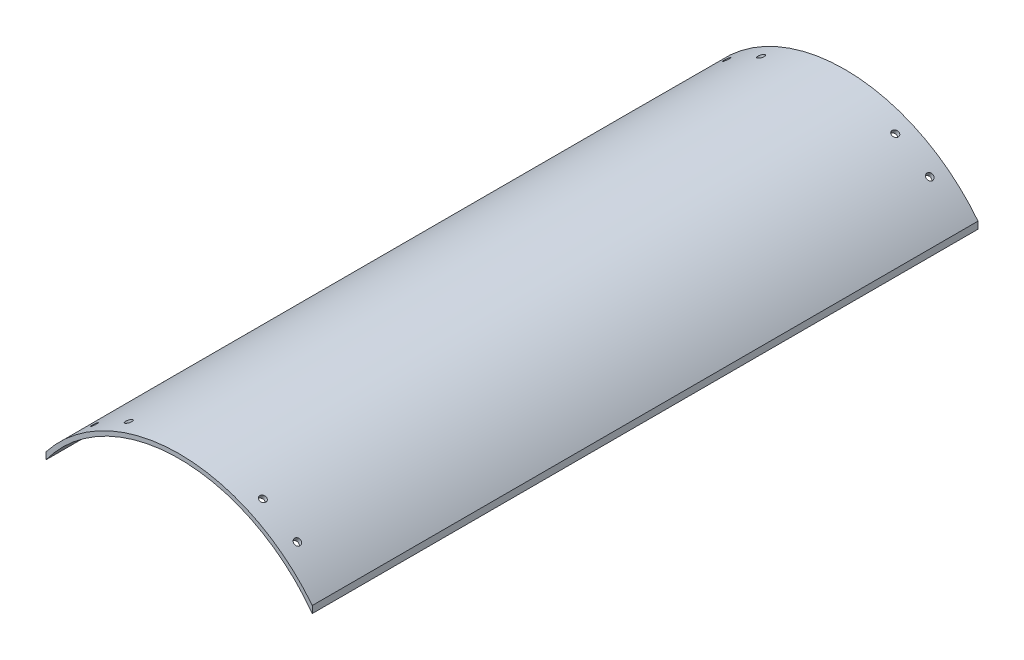
SolidWorks part; units mm, degrees
ref_plane "Front Plane" through (0, 0, 0) normal (0, 0, 1) x (1, 0, 0)
ref_plane "Top Plane" through (0, 0, 0) normal (0, 1, 0) x (1, 0, 0)
ref_plane "Right Plane" through (0, 0, 0) normal (1, 0, 0) x (0, 0, -1)
sketch "Sketch1" plane through (0, 0, 0) normal (0, 0, 1) x (1, 0, 0)
  line L0 (-40, 29.2099) -> (40, 29.2099)
  line L1 (-40, 29.2099) -> (-40, 31.3152)
  line L2 (40, 29.2099) -> (40, 31.3152)
  circle A0 centre (0, 0) radius 49.53
  circle A1 centre (0, 0) radius 50.8
  dimension "D1" = 101.6
  dimension "D2" = 1.27
  dimension "D3" = 80
extrude "Boss-Extrude1" add sketch "Sketch1" along normal blind 200 contours L2 A1 L1 A0
ref_plane "Plane2" through (0, 50.8, 0) normal (0, 1, 0) x (1, 0, 0)
ref_plane "Plane3" through (0, 0, 100) normal (0, 0, 1) x (1, 0, 0)
sketch "Sketch5" plane through (-693.2227, -633.3072, 0) normal (-0.7152, 0.6989, 0) x (0.6989, 0.7152, 0)
  line L0 (986.9759, 0) -> (930.3824, 0) construction
  line L3 (986.9759, 0) -> (930.3824, 0)
  line L8 (931.8881, -200) -> (931.8881, 0) construction
  line L9 (931.8881, -200) -> (931.8881, 0)
  circle A0 centre (937.4459, -144.6) radius 1.5
  circle A1 centre (937.4459, -170) radius 1.5
  circle A2 centre (937.4459, -30) radius 1.5
  circle A3 centre (937.4459, -55.4) radius 1.5
  point P4 (937.4222, -170)
  point P5 (940.8131, -170)
  point P12 (937.4459, -170)
  dimension "D1" = 3
  dimension "D2" = 25.4
  dimension "D4" = 30
  dimension "D5" = 25.4
  dimension "D6" = 30
extrude "Cut-Extrude2" cut sketch "Sketch5" against normal blind 9 contours A2 | A3 | A0 | A1 | A3 | A0 | A1
sketch "Sketch6" plane through (24.1451, 41.5821, -52.4) normal (-0.5021, -0.8648, 0) x (0, 0, 1)
  line L1 (252.4, -19.9237) -> (52.4, -19.9237) construction
  line L3 (152.4, -19.9237) -> (152.4, 71.1381) construction
  line L4 (252.4, -19.9237) -> (52.4, -19.9237)
  circle A0 centre (247.4, -6) radius 1
  circle A1 centre (247.4, 6) radius 1
  circle A2 centre (57.4, 6) radius 1
  circle A3 centre (57.4, -6) radius 1
  dimension "D1" = 2
  dimension "D2" = 2
extrude "Cut-Extrude3" cut sketch "Sketch6" against normal blind 7 contours A1 | A0 | A2 | A3
sketch "Sketch7" plane through (-24.1451, 41.5821, -52.4) normal (0.5021, -0.8648, 0) x (0.8648, 0.5021, 0)
  line L0 (-19.9237, 252.4) -> (-19.9237, 52.4) construction
  line L1 (-19.9237, 252.4) -> (-19.9237, 52.4)
  line L2 (-19.9237, 152.4) -> (58.7083, 152.4) construction
  circle A0 centre (6, 247.4) radius 1
  circle A1 centre (-6, 247.4) radius 1
  circle A2 centre (-6, 57.4) radius 1
  circle A3 centre (6, 57.4) radius 1
extrude "Cut-Extrude4" cut sketch "Sketch7" against normal blind 7 contours A1 | A0 | A2 | A3
